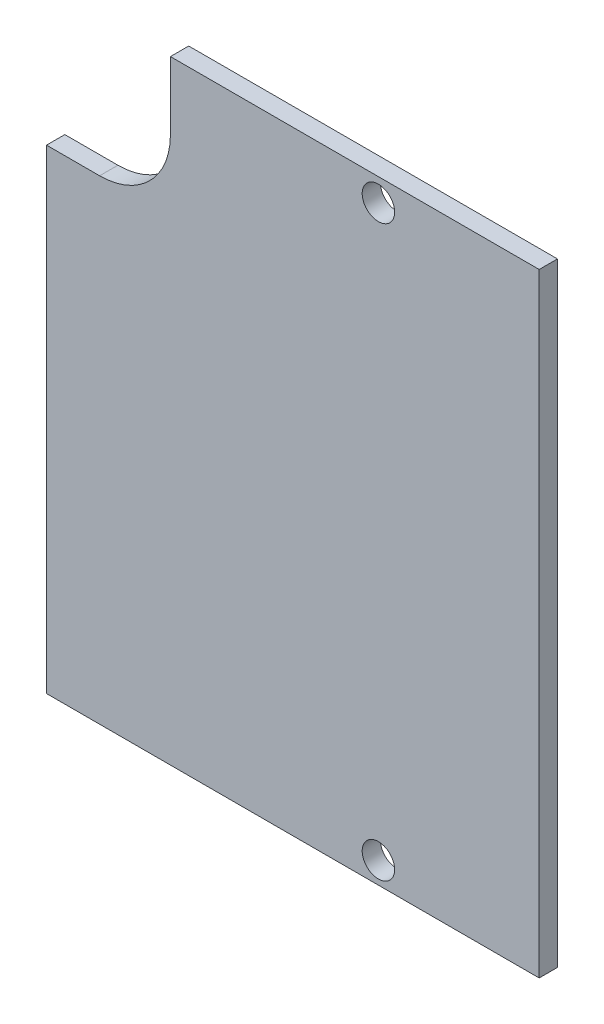
SolidWorks part; units mm, degrees
ref_plane "Front Plane" through (0, 0, 0) normal (0, 0, 1) x (1, 0, 0)
ref_plane "Top Plane" through (0, 0, 0) normal (0, 1, 0) x (1, 0, 0)
ref_plane "Right Plane" through (0, 0, 0) normal (1, 0, 0) x (0, 0, -1)
sketch "Sketch1" plane through (0, 0, 0) normal (0, 0, 1) x (1, 0, 0)
  line L0 (0, 0) -> (0, 52.832)
  line L1 (0, 52.832) -> (-31.75, 52.832)
  line L2 (-31.75, 52.832) -> (-31.75, 46.99)
  line L3 (-37.846, 40.894) -> (-42.418, 40.894)
  line L4 (-42.418, 40.894) -> (-42.418, 0)
  line L5 (-42.418, 0) -> (0, 0)
  arc A0 (-31.75, 46.99) -> (-37.846, 40.894) centre (-37.846, 46.99) cw
  circle A1 centre (-13.843, 50.8762) radius 1.397
  circle A2 centre (-13.843, 1.8542) radius 1.397
  point P13 (0, 0)
  dimension "D1" = 52.832
  dimension "D6" = 2.794
  dimension "D2" = 42.418
  dimension "D3" = 10.668
  dimension "D4" = 46.99
  dimension "D5" = 4.572
  dimension "D7" = 50.8762
  dimension "D8" = 1.8542
  dimension "D9" = 28.575
extrude "Boss-Extrude1" add sketch "Sketch1" along normal blind 1.5748
